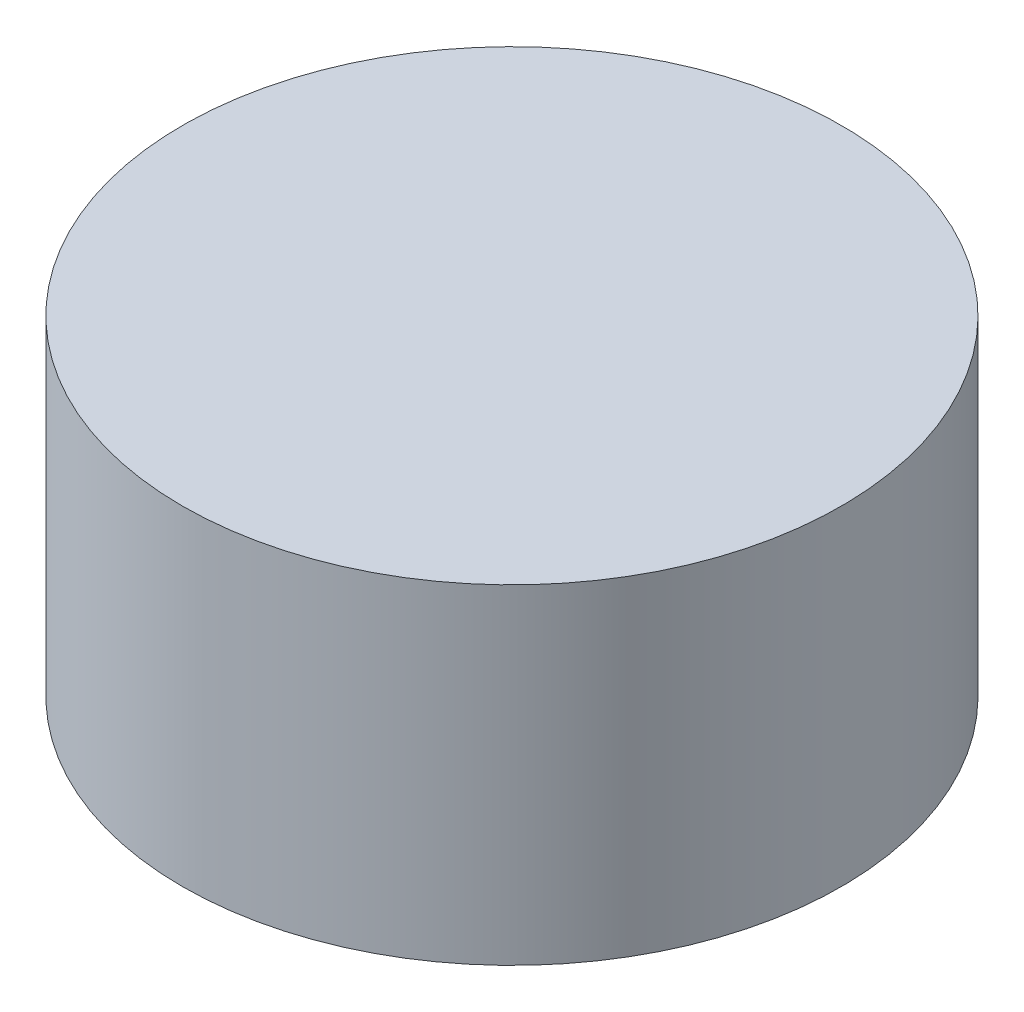
SolidWorks part; units mm, degrees
ref_plane "Front Plane" through (0, 0, 0) normal (0, 0, 1) x (1, 0, 0)
ref_plane "Top Plane" through (0, 0, 0) normal (0, 1, 0) x (1, 0, 0)
ref_plane "Right Plane" through (0, 0, 0) normal (1, 0, 0) x (0, 0, -1)
sketch "Sketch1" plane through (0, 0, 0) normal (0, 1, 0) x (1, 0, 0)
  circle A0 centre (0, 0) radius 1.5
extrude "Boss-Extrude1" add sketch "Sketch1" along normal blind 1.5
